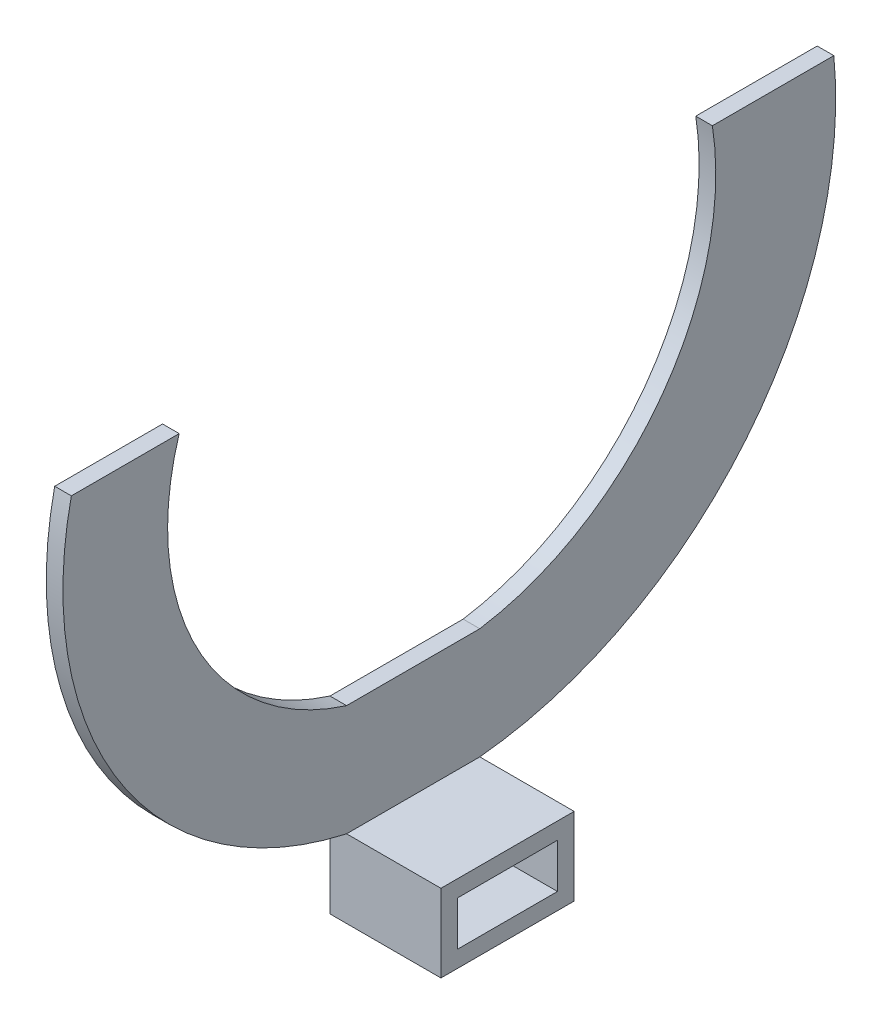
SolidWorks part; units mm, degrees
ref_plane "Front Plane" through (0, 0, 0) normal (0, 0, 1) x (1, 0, 0)
ref_plane "Top Plane" through (0, 0, 0) normal (0, 1, 0) x (1, 0, 0)
ref_plane "Right Plane" through (0, 0, 0) normal (1, 0, 0) x (0, 0, -1)
sketch "Sketch1" plane through (0, 0, 0) normal (1, 0, 0) x (0, 0, -1)
  line L0 (3, 3) -> (21, 3)
  line L1 (0, 0) -> (24, 0)
  line L2 (0, 0) -> (0, 14)
  line L3 (0, 14) -> (24, 14)
  line L4 (24, 0) -> (24, 14)
  line L5 (21, 3) -> (21, 11)
  line L6 (3, 11) -> (21, 11)
  line L7 (3, 3) -> (3, 11)
  dimension "D1" = 24
  dimension "D2" = 14
  dimension "D3" = 3
extrude "Boss-Extrude1" add sketch "Sketch1" along normal blind 20
sketch "Sketch3" plane through (0, 14, 0) normal (0, 1, 0) x (1, 0, 0)
  line L0 (20, 0) -> (0, 0) construction
  line L1 (0, 24) -> (3, 24)
  line L2 (0, 24) -> (0, 0)
  line L3 (0, 0) -> (3, 0)
  line L4 (3, 24) -> (3, 0)
  dimension "D1" = 3
extrude "Boss-Extrude2" add sketch "Sketch3" along normal blind 20
sketch "Sketch5" plane through (3, 0, 0) normal (1, 0, 0) x (0, 0, -1)
  line L0 (-49.5923, 91.529) -> (-30.1601, 91.529)
  line L1 (65.9097, 91.529) -> (87.7921, 91.529)
  line L2 (0, 34) -> (0, 14)
  line L3 (24, 34) -> (24, 14)
  arc A0 (0, 34) -> (-30.1601, 91.529) centre (13.6844, 77.8446) cw
  arc A1 (0, 14) -> (-49.5923, 91.529) centre (13.9684, 77.5606) cw
  arc A2 (24, 34) -> (65.9097, 91.529) centre (16.1903, 83.7193) ccw
  arc A3 (24, 14) -> (87.7921, 91.529) centre (17.1316, 84.6606) ccw
extrude "Boss-Extrude4" add sketch "Sketch5" against normal blind 3
